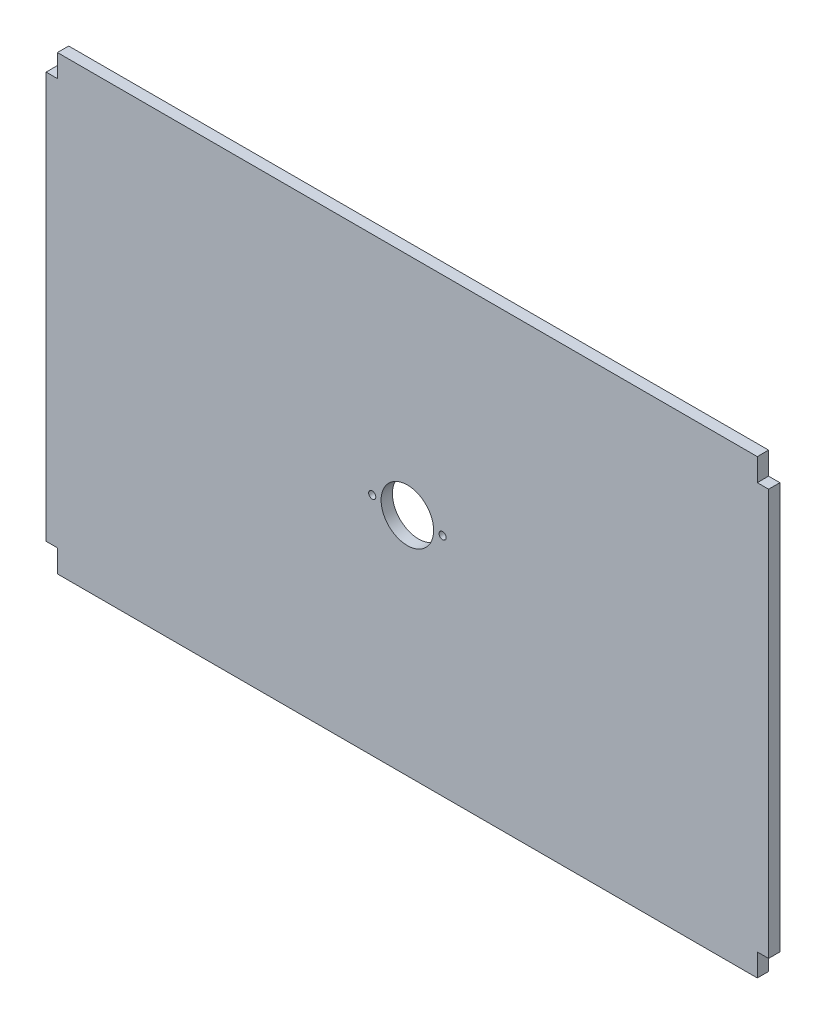
SolidWorks part; units mm, degrees
ref_plane "Front" through (0, 0, 0) normal (0, 0, 1) x (1, 0, 0)
ref_plane "Top" through (0, 0, 0) normal (0, 1, 0) x (1, 0, 0)
ref_plane "Right" through (0, 0, 0) normal (1, 0, 0) x (0, 0, -1)
sketch "Sketch2" plane through (0, 0, 0) normal (0, 0, 1) x (1, 0, 0)
  line L0 (0, 120.65) -> (0, 127)
  line L1 (0, 0) -> (196.85, 0)
  line L2 (0, 0) -> (0, 6.35)
  line L3 (0, 127) -> (196.85, 127)
  line L4 (196.85, 0) -> (196.85, 6.35)
  line L5 (0, 6.35) -> (-3.175, 6.35)
  line L7 (0, 120.65) -> (-3.175, 120.65)
  line L8 (-3.175, 6.35) -> (-3.175, 120.65)
  line L9 (196.85, 6.35) -> (200.025, 6.35)
  line L11 (196.85, 120.65) -> (200.025, 120.65)
  line L12 (200.025, 6.35) -> (200.025, 120.65)
  line L13 (196.85, 120.65) -> (196.85, 127)
  dimension "D1" = 127
  dimension "D2" = 196.85
  dimension "D3" = 3.175
  dimension "D4" = 3.175
  dimension "D5" = 114.3
  dimension "D6" = 114.3
  dimension "D7" = 6.35
  dimension "D8" = 6.35
extrude "Boss-Extrude1" add sketch "Sketch2" along normal blind 3.175
sketch "Sketch3" plane through (0, 0, 3.175) normal (0, 0, 1) x (1, 0, 0)
  line L0 (-3.175, 63.5) -> (200.025, 63.5) construction
  line L1 (-3.175, 120.65) -> (-3.175, 6.35) construction
  line L2 (200.025, 6.35) -> (200.025, 120.65) construction
  line L3 (98.425, 0) -> (98.425, 127) construction
  line L4 (0, 0) -> (196.85, 0) construction
  line L5 (196.85, 127) -> (0, 127) construction
  circle A0 centre (98.425, 63.5) radius 7.39
  circle A1 centre (88.545, 63.5) radius 1
  circle A2 centre (108.357, 63.5) radius 1
  dimension "D1" = 2
  dimension "D2" = 19.812
  dimension "D3" = 14.78
  dimension "D4" = 9.88
extrude "Cut-Extrude1" cut sketch "Sketch3" against normal through all
